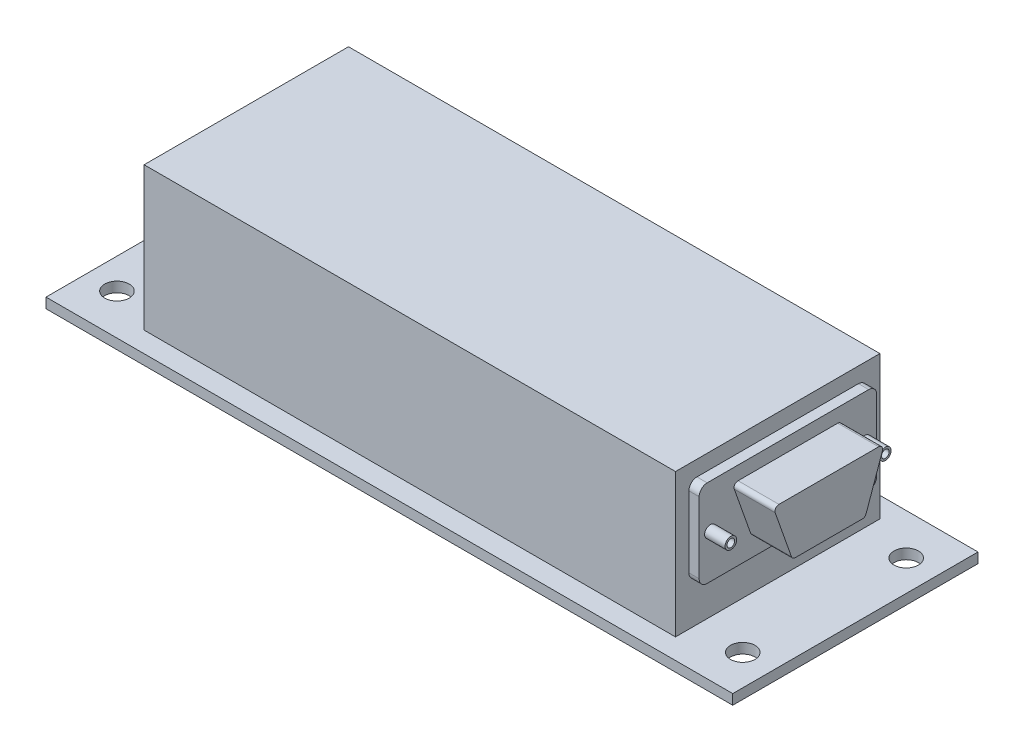
SolidWorks part; units mm, degrees
ref_plane "Front Plane" through (0, 0, 0) normal (0, 0, 1) x (1, 0, 0)
ref_plane "Top Plane" through (0, 0, 0) normal (0, 1, 0) x (1, 0, 0)
ref_plane "Right Plane" through (0, 0, 0) normal (1, 0, 0) x (0, 0, -1)
sketch "Sketch2" plane through (0, 0, 0) normal (0, 1, 0) x (1, 0, 0)
  line L0 (-53.34, -19.05) -> (53.34, -19.05)
  line L1 (-53.34, -19.05) -> (-53.34, 19.05)
  line L2 (53.34, -19.05) -> (53.34, 19.05)
  line L3 (-53.34, 19.05) -> (53.34, 19.05)
  line L4 (-53.34, -19.05) -> (53.34, 19.05) construction
  line L5 (53.34, -19.05) -> (-53.34, 19.05) construction
  point P1 (0, 0)
extrude "Boss-Extrude1" add sketch "Sketch2" against normal blind 1.5748
sketch "Sketch3" plane through (0, 0, 0) normal (0, 1, 0) x (1, 0, 0)
  line L0 (53.34, 19.05) -> (-53.34, 19.05) construction
  line L1 (53.34, -19.05) -> (53.34, 19.05) construction
  line L2 (48.5775, 19.05) -> (-48.636, 19.05) construction
  line L3 (53.34, -12.7313) -> (53.34, 12.6603) construction
  line L4 (-946.66, 12.6603) -> (49053.34, 12.6603) construction
  line L5 (-946.66, -12.7313) -> (49053.34, -12.7313) construction
  line L6 (-48.636, -980.95) -> (-48.636, 49019.05) construction
  line L7 (48.5775, -980.95) -> (48.5775, 49019.05) construction
  circle A0 centre (-48.636, 12.6603) radius 1.9
  circle A1 centre (-48.636, -12.7313) radius 1.9
  circle A2 centre (48.5775, 12.6603) radius 1.9
  circle A3 centre (48.5775, -12.7313) radius 1.9
  point P0 (0, 19.05)
  point P1 (53.34, 0)
  point P4 (-48.5775, 19.05)
  point P7 (53.34, 12.7)
  point P10 (-0.0292, 19.05)
  point P11 (53.34, 12.7)
  point P15 (53.34, -0.0355)
  dimension "D1" = 48.5775
  dimension "D2" = 12.7
extrude "Cut-Extrude1" cut sketch "Sketch3" against normal through all
sketch "Sketch4" plane through (0, 0, 0) normal (0, 1, 0) x (1, 0, 0)
  line L1 (-41.275, -15.875) -> (41.275, -15.875)
  line L2 (-41.275, -15.875) -> (-41.275, 15.875)
  line L3 (-41.275, 15.875) -> (41.275, 15.875)
  line L4 (41.275, -15.875) -> (41.275, 15.875)
  line L5 (-41.275, -15.875) -> (41.275, 15.875) construction
  line L6 (-41.275, 15.875) -> (41.275, -15.875) construction
  point P0 (0, 0)
  point P1 (0, 0)
extrude "Boss-Extrude2" add sketch "Sketch4" along normal blind 22.2504
sketch "Sketch5" plane through (41.275, 0, 0) normal (1, 0, 0) x (0, 0, -1)
  line L0 (-1000, 11.1252) -> (49000, 11.1252) construction
  line L1 (-15.875, 0) -> (15.875, 0)
  line L2 (-15.875, 0) -> (-15.875, 22.2504)
  line L3 (-15.875, 22.2504) -> (15.875, 22.2504)
  line L4 (15.875, 0) -> (15.875, 22.2504)
  line L5 (0, -988.8748) -> (0, 49011.1252) construction
  line L7 (-12.5432, 6.3267) -> (12.5432, 6.3267)
  line L8 (-13.7932, 7.5767) -> (-13.7932, 18.6102)
  line L9 (-12.5432, 19.8602) -> (12.5432, 19.8602)
  line L10 (13.7932, 7.5767) -> (13.7932, 18.6102)
  line L11 (-13.7932, 6.3267) -> (13.7932, 19.8602) construction
  line L12 (-13.7932, 19.8602) -> (13.7932, 6.3267) construction
  arc A0 (13.7932, 7.5767) -> (12.5432, 6.3267) centre (12.5432, 7.5767) cw
  arc A1 (-13.7932, 7.5767) -> (-12.5432, 6.3267) centre (-12.5432, 7.5767) ccw
  arc A2 (-13.7932, 18.6102) -> (-12.5432, 19.8602) centre (-12.5432, 18.6102) cw
  arc A3 (12.5432, 19.8602) -> (13.7932, 18.6102) centre (12.5432, 18.6102) cw
  point P6 (0, 11.1252)
  point P10 (0, 0)
  point P12 (0, 22.2504)
  point P14 (0, 13.0935)
  point P19 (0, 0)
  dimension "D1" = 1.25
extrude "Boss-Extrude3" add sketch "Sketch5" along normal blind 1.5875 contours L9 A3 L10 A0 L7 A1 L8 A2
sketch "Sketch7" plane through (42.8625, 0, 0) normal (1, 0, 0) x (0, 0, -1)
  line L0 (13.7932, 7.5767) -> (13.7932, 18.6102) construction
  line L1 (-12.5432, 6.3267) -> (12.5432, 6.3267) construction
  line L2 (-1000, 13.0935) -> (49000, 13.0935) construction
  line L3 (-12.0387, 13.0935) -> (11.9613, 13.0935) construction
  circle A0 centre (11.9613, 13.0935) radius 0.6
  circle A1 centre (11.9613, 13.0935) radius 0.9
  circle A2 centre (-12.0387, 13.0935) radius 0.6
  circle A3 centre (-12.0387, 13.0935) radius 0.9
  point P0 (13.7932, 13.0935)
  point P1 (0, 6.3267)
  point P4 (-0.0387, 13.0935)
  point P12 (-0.0387, 13.0935)
extrude "Boss-Extrude4" add sketch "Sketch7" along normal blind 3.175
sketch "Sketch8" plane through (42.8625, 0, 0) normal (1, 0, 0) x (0, 0, -1)
  line L0 (-12.5432, 19.8602) -> (12.5432, 19.8602) construction
  line L1 (13.7932, 7.5767) -> (13.7932, 18.6102) construction
  line L2 (-1000, 13.0935) -> (49000, 13.0935) construction
  line L3 (0, -986.9065) -> (0, 49013.0935) construction
  line L4 (-8.6255, 17.7393) -> (8.6255, 17.7393) construction
  line L5 (-5.65, 9.3009) -> (5.65, 9.3009) construction
  line L6 (-8.3318, 16.9065) -> (-5.7971, 9.7181)
  line L7 (-5.2076, 9.3009) -> (5.2076, 9.3009)
  line L8 (5.7971, 9.7181) -> (8.3318, 16.9065)
  line L9 (7.7424, 17.7393) -> (-7.7424, 17.7393)
  arc A0 (-5.2076, 9.3009) -> (-5.7971, 9.7181) centre (-5.2076, 9.9259) cw
  arc A1 (7.7424, 17.7393) -> (8.3318, 16.9065) centre (7.7424, 17.1143) cw
  arc A2 (5.7971, 9.7181) -> (5.2076, 9.3009) centre (5.2076, 9.9259) cw
  arc A3 (-8.3318, 16.9065) -> (-7.7424, 17.7393) centre (-7.7424, 17.1143) cw
  point P0 (-0.099, 19.8602)
  point P1 (13.7932, 13.0935)
  point P4 (0, 13.0935)
  point P14 (0, 17.7393)
  point P18 (0, 9.3009)
  dimension "D1" = 0.625
extrude "Boss-Extrude5" add sketch "Sketch8" along normal blind 6.35
